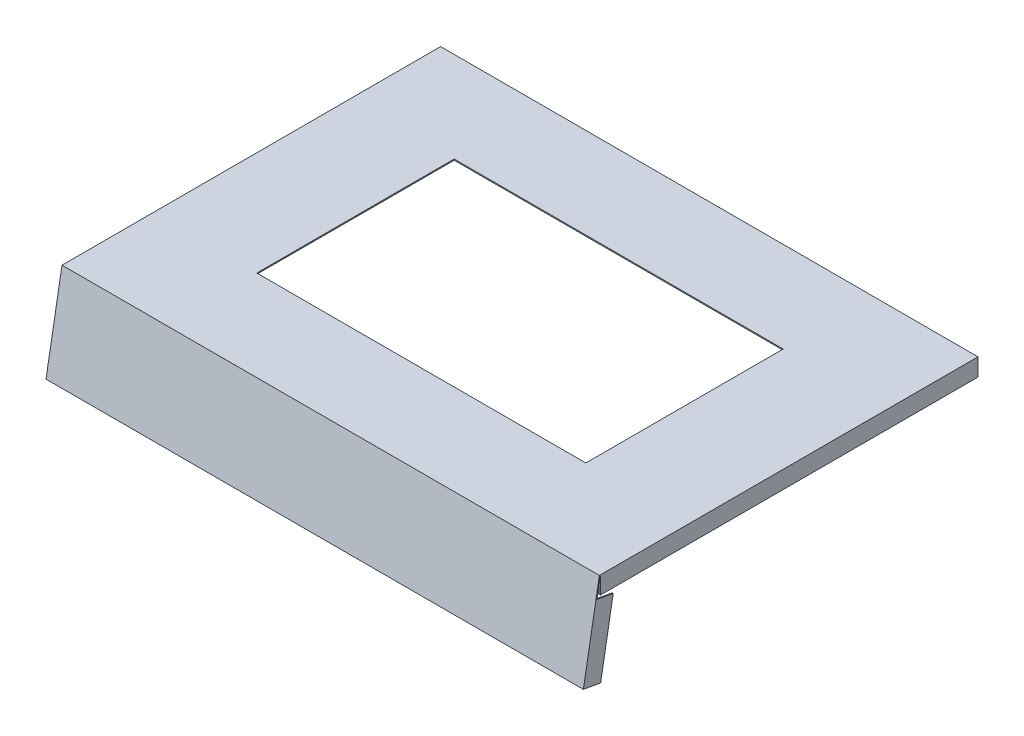
SolidWorks part; units mm, degrees
ref_plane "Alzado" through (0, 0, 0) normal (0, 0, 1) x (1, 0, 0)
ref_plane "Planta" through (0, 0, 0) normal (0, 1, 0) x (1, 0, 0)
ref_plane "Vista lateral" through (0, 0, 0) normal (1, 0, 0) x (0, 0, -1)
sketch "Croquis1" plane through (0, 0, 0) normal (0, 1, 0) x (1, 0, 0)
  line L1 (-245, -172.625) -> (245, -172.625)
  line L2 (-245, -172.625) -> (-245, 172.625)
  line L3 (-245, 172.625) -> (245, 172.625)
  line L4 (245, -172.625) -> (245, 172.625)
  line L5 (-245, -172.625) -> (245, 172.625) construction
  line L6 (-245, 172.625) -> (245, -172.625) construction
  point P0 (0, 0)
  dimension "D1" = 490
  dimension "D2" = 345.25
extrude "Saliente-Extruir1" add sketch "Croquis1" along normal blind 1
sketch "Croquis2" plane through (0, 1, 0) normal (0, 1, 0) x (1, 0, 0)
  line L1 (-150, -90) -> (150, -90)
  line L2 (-150, -90) -> (-150, 90)
  line L3 (-150, 90) -> (150, 90)
  line L4 (150, -90) -> (150, 90)
  line L5 (-150, -90) -> (150, 90) construction
  line L6 (-150, 90) -> (150, -90) construction
  point P0 (0, 0)
  dimension "D1" = 300
  dimension "D2" = 180
extrude "Cortar-Extruir1" cut sketch "Croquis2" against normal through all
sketch "Croquis3" plane through (245, 0, 0) normal (1, 0, 0) x (0, 0, -1)
  line L1 (-172.625, 1) -> (-187.2114, -81.7239)
  line L2 (-173.6035, 1) -> (-179.356, 1) construction
  line L3 (-172.625, 1) -> (172.625, 1) construction
  line L6 (-187.2114, -81.7239) -> (-186.2266, -81.8975)
  line L11 (-186.2266, -81.8975) -> (-171.6096, 1)
  line L13 (-171.6096, 1) -> (-172.625, 1)
  dimension "D1" = 80
  dimension "D2" = 84
  dimension "D3" = 1
extrude "Saliente-Extruir2" add sketch "Croquis3" against normal through all
sketch "Croquis4" plane through (0, 0, 0) normal (0, -1, 0) x (1, 0, 0)
  line L0 (-245, 171.7859) -> (245, 171.7859) construction
  line L2 (-245, -172.625) -> (-245, 171.7859)
  line L3 (-245, 171.7859) -> (-244, 171.7859)
  line L4 (-244, -171.625) -> (-244, 171.7859)
  line L7 (245, -172.625) -> (245, 171.7859)
  line L8 (245, 171.7859) -> (244, 171.7859)
  line L9 (244, -171.625) -> (244, 171.7859)
  line L10 (-244, -171.625) -> (244, -171.625)
  line L12 (-245, -172.625) -> (245, -172.625)
  dimension "D1" = 1
  dimension "D2" = 1
  dimension "D3" = 1
extrude "Saliente-Extruir3" add sketch "Croquis4" along normal blind 15
sketch "Croquis5" plane through (0, 29.3771, 166.6059) normal (0, -0.1736, -0.9848) x (-1, 0, 0)
  line L0 (-245, -112.9912) -> (-245, -29.8303) construction
  line L1 (-244, -111.9912) -> (-244, -46.9912)
  line L2 (-245, -46.9912) -> (-245, -112.9912)
  line L3 (-245, -112.9912) -> (245, -112.9912)
  line L4 (245, -46.9912) -> (245, -112.9912)
  line L5 (-244, -46.9912) -> (-245, -46.9912)
  line L6 (-244, -111.9912) -> (244, -111.9912)
  line L7 (244, -111.9912) -> (244, -46.9912)
  line L8 (244, -46.9912) -> (245, -46.9912)
  line L9 (-245, -46.9912) -> (245, -46.9912) construction
  line L10 (-244, -47.9912) -> (244, -47.9912) construction
  line L11 (-244, -47.9912) -> (-244, -111.9912) construction
  line L12 (244, -47.9912) -> (244, -111.9912) construction
  dimension "D2" = 65
  dimension "D1" = 1
extrude "Saliente-Extruir4" add sketch "Croquis5" along normal blind 15
sketch "Croquis6" plane through (-245, 0, 0) normal (-1, 0, 0) x (0, 0, 1)
  line L0 (-166.625, -15) -> (-166.625, 1) construction
  line L1 (171.7859, -15) -> (-172.625, -15) construction
  line L2 (-172.625, 1) -> (172.625, 1) construction
  line L3 (-172.625, 1) -> (-172.625, -15) construction
  circle A0 centre (-166.625, -7) radius 1.5
  dimension "D2" = 3
  dimension "D1" = 6
extrude "Saliente-Extruir5" add sketch "Croquis6" along normal blind 3
